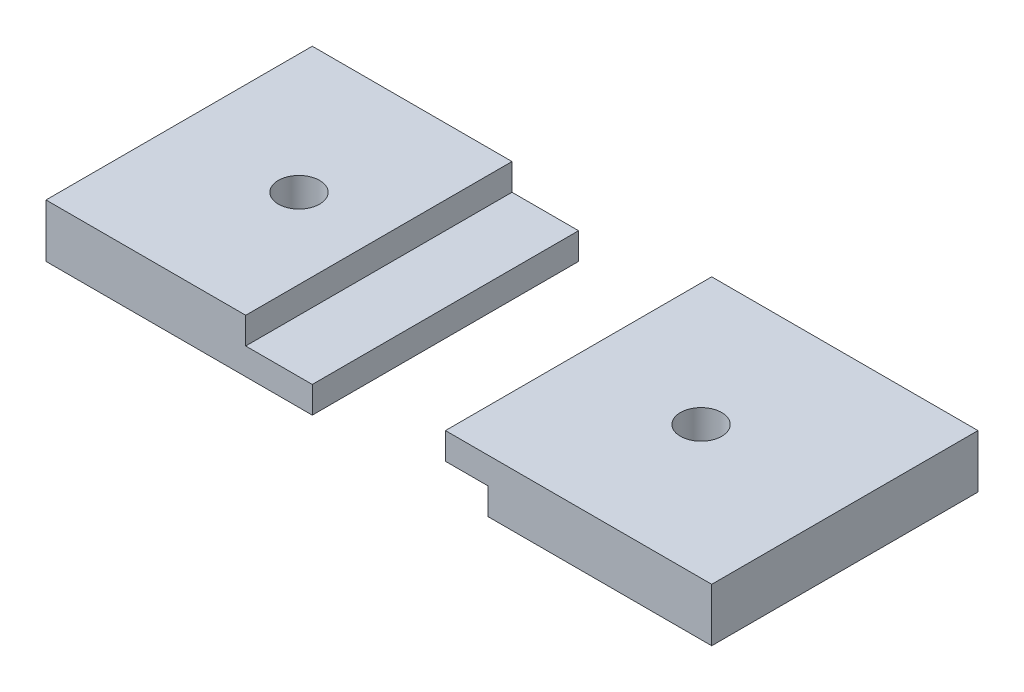
SolidWorks part; units mm, degrees
ref_plane "Front Plane" through (0, 0, 0) normal (0, 0, 1) x (1, 0, 0)
ref_plane "Top Plane" through (0, 0, 0) normal (0, 1, 0) x (1, 0, 0)
ref_plane "Right Plane" through (0, 0, 0) normal (1, 0, 0) x (0, 0, -1)
sketch "Sketch1" plane through (0, 0, 0) normal (0, 1, 0) x (1, 0, 0)
  line L1 (0, 0) -> (-20, 0)
  line L2 (0, 0) -> (0, 20)
  line L3 (0, 20) -> (-20, 20)
  line L4 (-20, 0) -> (-20, 20)
  line L5 (10, 0) -> (30, 0)
  line L6 (10, 0) -> (10, 20)
  line L7 (10, 20) -> (30, 20)
  line L8 (30, 0) -> (30, 20)
  dimension "D1" = 20
  dimension "D2" = 20
  dimension "D3" = 20
  dimension "D4" = 20
extrude "Boss-Extrude1" add sketch "Sketch1" along normal blind 4
sketch "Sketch2" plane through (0, 0, 0) normal (1, 0, 0) x (0, 0, -1)
  line L0 (20, 4) -> (20, 0) construction
  line L1 (0, 4) -> (20, 4)
  line L2 (0, 4) -> (0, 2)
  line L3 (0, 2) -> (20, 2)
  line L4 (20, 4) -> (20, 2)
extrude "Cut-Extrude1" cut sketch "Sketch2" against normal blind 5
sketch "Sketch3" plane through (10, 0, 0) normal (-1, 0, 0) x (0, 0, 1)
  line L0 (0, 4) -> (0, 0) construction
  line L1 (-20, 0) -> (0, 0)
  line L2 (-20, 0) -> (-20, 2)
  line L3 (-20, 2) -> (0, 2)
  line L4 (0, 0) -> (0, 2)
extrude "Cut-Extrude2" cut sketch "Sketch3" against normal blind 3.2
sketch "Sketch5" plane through (0, 4, 0) normal (0, 1, 0) x (1, 0, 0)
  line L0 (-5, 20) -> (-20, 20) construction
  line L2 (-5, 0) -> (-5, 20) construction
  circle A0 centre (-11, 10) radius 1.55
  dimension "D1" = 3.1
  dimension "D2" = 10
  dimension "D3" = 6
extrude "Cut-Extrude3" cut sketch "Sketch5" against normal blind 4
sketch "Sketch6" plane through (0, 4, 0) normal (0, 1, 0) x (1, 0, 0)
  line L0 (30, 20) -> (10, 20) construction
  line L1 (13.2, 0) -> (13.2, 20) construction
  circle A0 centre (19.2, 10) radius 1.55
  dimension "D1" = 3.1
  dimension "D2" = 10
  dimension "D3" = 6
extrude "Cut-Extrude4" cut sketch "Sketch6" against normal blind 4
